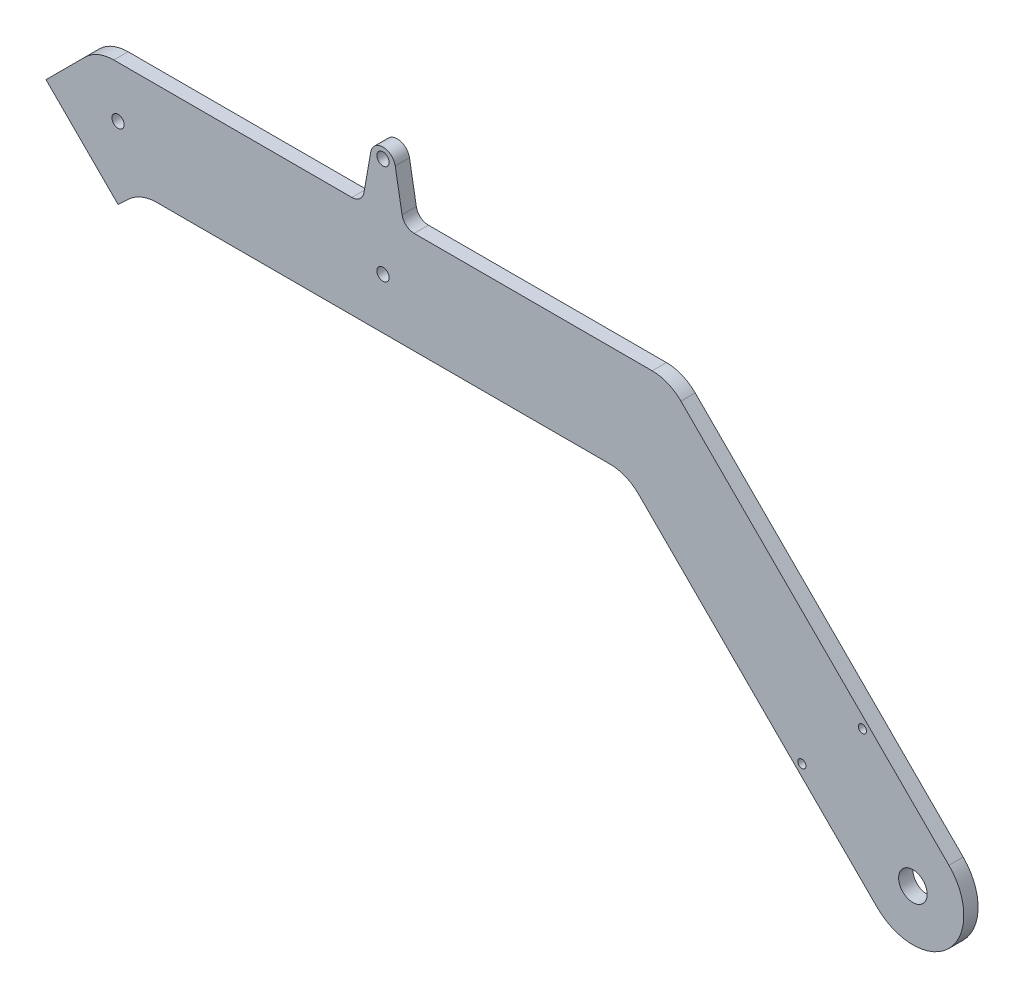
SolidWorks part; units mm, degrees
material "Acrylic (Medium-high impact)"
ref_plane "Front Plane" through (0, 0, 0) normal (0, 0, 1) x (1, 0, 0)
ref_plane "Top Plane" through (0, 0, 0) normal (0, 1, 0) x (1, 0, 0)
ref_plane "Right Plane" through (0, 0, 0) normal (1, 0, 0) x (0, 0, -1)
sketch "Sketch1" plane through (0, 0, 0) normal (0, 0, 1) x (1, 0, 0)
  line L0 (65, 0) -> (-65, 0) construction
  line L1 (-65, 0) -> (0, 65) construction
  line L2 (0, 65) -> (65, 0) construction
  line L3 (0, 65) -> (130, 65) construction
  line L4 (130, 65) -> (195, 0) construction
  circle A0 centre (-65, 0) radius 30
  circle A1 centre (65, 0) radius 30
  circle A2 centre (195, 0) radius 30
  point P4 (0, 0)
  dimension "D2" = 60
  dimension "D1" = 130
  dimension "D3" = 90
  dimension "D4" = 91.9239
  dimension "D5" = 135
  dimension "D6" = 130
sketch "Sketch2" plane through (0, 0, 0) normal (0, 0, 1) x (1, 0, 0)
  line L4 (-56.1612, -8.8388) -> (0, 47.3223)
  line L5 (0, 47.3223) -> (56.1612, -8.8388)
  line L6 (-73.8388, 8.8388) -> (0, 82.6777)
  line L7 (0, 82.6777) -> (73.8388, 8.8388)
  line L19 (56.1612, -8.8388) -> (0, 47.3223)
  circle A0 centre (-65, 0) radius 3.5
  circle A1 centre (65, 0) radius 3.5
  arc A4 (56.1612, -8.8388) -> (73.8388, 8.8388) centre (65, 0) ccw
  arc A5 (-73.8388, 8.8388) -> (-56.1612, -8.8388) centre (-65, 0) ccw
  circle A6 centre (65, 0) radius 3.5
  circle A7 centre (0, 65) radius 1.5
  point P18 (-65, 0)
  dimension "D6" = 3
  dimension "D1" = 25
  dimension "D2" = 90
sketch "Sketch3" plane through (0, 0, 0) normal (0, 0, 1) x (1, 0, 0)
  line L0 (5.5594, 52.5) -> (0, 47.3223)
  line L1 (-56.1612, -8.8388) -> (0, 47.3223) construction
  line L2 (-73.8388, 8.8388) -> (0, 82.6777) construction
  line L3 (0, 47.3223) -> (-17.6777, 65)
  line L4 (5.5594, 52.5) -> (124.8223, 52.5)
  line L5 (124.8223, 52.5) -> (186.1612, -8.8388)
  line L6 (-5.1777, 77.5) -> (59.8841, 77.5)
  line L7 (135.1777, 77.5) -> (203.8388, 8.8388)
  line L8 (-17.6777, 65) -> (-5.1777, 77.5)
  line L9 (0, 65) -> (130, 65) construction
  line L10 (0, 47.3223) -> (56.1612, -8.8388) construction
  line L11 (65, 77.5) -> (65, 89.5) construction
  line L12 (59.8841, 77.5) -> (62, 89.5)
  line L13 (70.1159, 77.5) -> (68, 89.5)
  line L14 (70.1159, 77.5) -> (135.1777, 77.5)
  arc A0 (203.8388, 8.8388) -> (186.1612, -8.8388) centre (195, 0) cw
  circle A1 centre (195, 0) radius 3.5
  circle A2 centre (65, 0) radius 3.5 construction
  circle A3 centre (0, 65) radius 1.5
  circle A5 centre (65, 65) radius 1.5
  circle A6 centre (65, 89.5) radius 1.5
  arc A7 (68, 89.5) -> (62, 89.5) centre (65, 88.971) ccw
  dimension "D2" = 3
  dimension "D6" = 3
  dimension "D8" = 12.5
  dimension "D1" = 25
  dimension "D3" = 12
  dimension "D4" = 80
  dimension "D5" = 3
  dimension "D7" = 25
extrude "Boss-Extrude1" add sketch "Sketch3" along normal blind 3.5
fillet "Fillet1" radius 10 4 edges at (124.8223, 52.5, 1.75) (5.5594, 52.5, 1.75) (-5.1777, 77.5, 1.75) (135.1777, 77.5, 1.75)
fillet "Fillet2" radius 3 2 edges at (59.8841, 77.5, 1.75) (70.1159, 77.5, 1.75)
sketch "Sketch4" plane through (0, 0, 0) normal (0, 0, -1) x (-1, 0, 0)
  line L0 (-195, 0) -> (-175.201, 19.799) construction
  line L1 (-127.7513, 49.5711) -> (-186.1612, -8.8388) construction
  line L2 (-167.7764, 12.3744) -> (-182.6256, 27.2236) construction
  circle A0 centre (-167.7764, 12.3744) radius 1
  circle A1 centre (-182.6256, 27.2236) radius 1
  point P8 (-175.201, 19.799)
  dimension "D3" = 2
  dimension "D1" = 28
  dimension "D2" = 2
extrude "Cut-Extrude1" cut sketch "Sketch4" against normal blind 10
